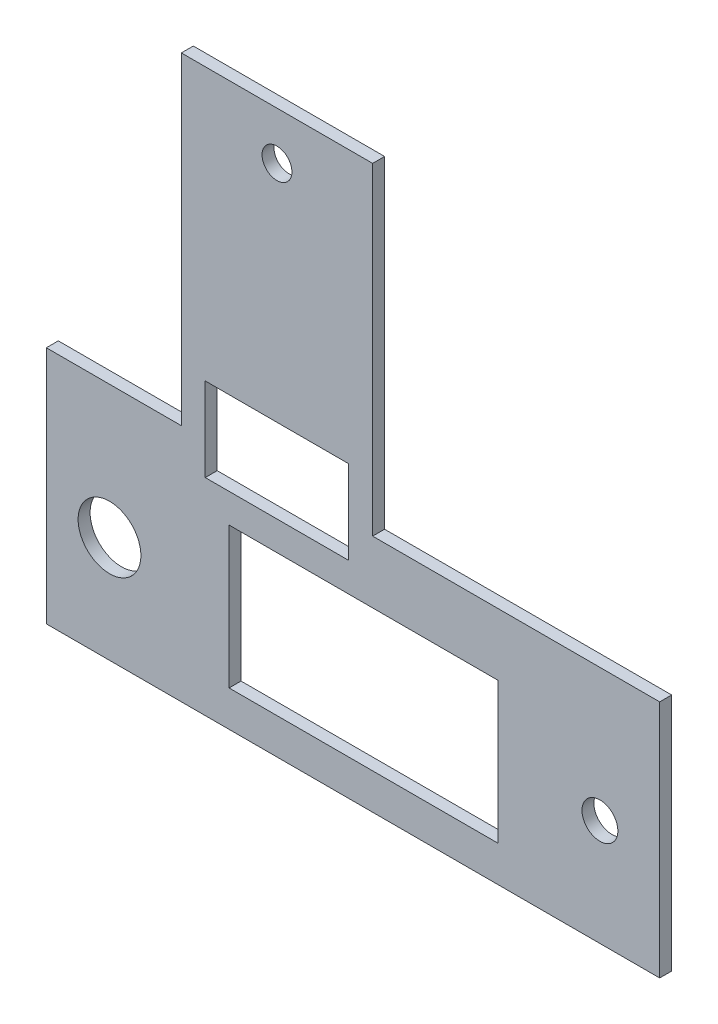
SolidWorks part; units mm, degrees
ref_plane "Alzado" through (0, 0, 0) normal (0, 0, 1) x (1, 0, 0)
ref_plane "Planta" through (0, 0, 0) normal (0, 1, 0) x (1, 0, 0)
ref_plane "Vista lateral" through (0, 0, 0) normal (1, 0, 0) x (0, 0, -1)
sketch "Croquis1" plane through (0, 0, 0) normal (0, 0, 1) x (1, 0, 0)
  line L0 (0.6829, 8.5049) -> (0.6829, 35.5049)
  line L1 (-10.6071, 8.5049) -> (0.6829, 8.5049)
  line L2 (-10.6071, 8.5049) -> (-10.6071, -11.4951)
  line L3 (-10.6071, -11.4951) -> (40.6907, -11.4951)
  line L4 (40.6907, 8.5049) -> (40.6907, -11.4951)
  line L5 (4.6761, 3.3049) -> (27.1761, 3.3049)
  line L6 (4.6761, 3.3049) -> (4.6761, -8.4951)
  line L7 (4.6761, -8.4951) -> (27.1761, -8.4951)
  line L8 (27.1761, 3.3049) -> (27.1761, -8.4951)
  line L9 (15.0418, 8.5049) -> (15.0418, -11.4951) construction
  line L10 (0.6829, 35.5049) -> (16.6829, 35.5049)
  line L11 (16.6829, 35.5049) -> (16.6829, 8.5049)
  line L12 (16.6829, 8.5049) -> (40.6907, 8.5049)
  line L13 (8.6829, -11.4951) -> (8.6829, 27.8056) construction
  line L14 (2.6829, 12.7461) -> (14.6829, 12.7461)
  line L15 (2.6829, 12.7461) -> (2.6829, 5.7461)
  line L16 (2.6829, 5.7461) -> (14.6829, 5.7461)
  line L17 (14.6829, 12.7461) -> (14.6829, 5.7461)
  circle A0 centre (8.6829, 31.5049) radius 1.25
  circle A9 centre (-5.3239, -2.5951) radius 2.625
  circle A10 centre (35.6907, -2.5951) radius 1.5
  dimension "D4" = 20
  dimension "D8" = 7
  dimension "D9" = 12
  dimension "D11" = 5.9
  dimension "D10" = 5.9
  dimension "D12" = 5
  dimension "D13" = 2
  dimension "D3" = 11.29
  dimension "D14" = 27
  dimension "D15" = 4
  dimension "D16" = 3
  dimension "D17" = 10
  dimension "D5" = 16
  dimension "D6" = 22.5
  dimension "D7" = 11.8
  dimension "D18" = 8.5146
  dimension "D19" = 4.0068
extrude "Saliente-Extruir1" add sketch "Croquis1" along normal blind 1
